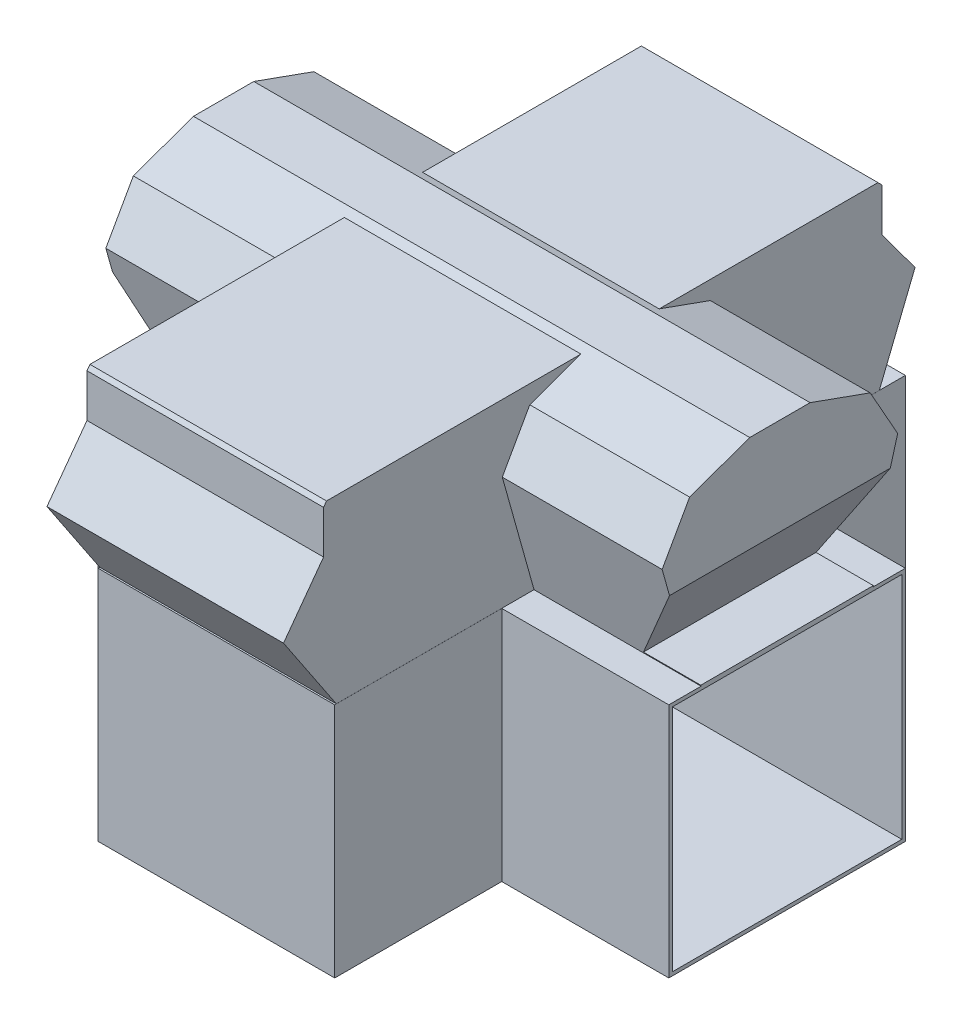
SolidWorks part; units mm, degrees
ref_plane "Front Plane" through (0, 0, 0) normal (0, 0, 1) x (1, 0, 0)
ref_plane "Top Plane" through (0, 0, 0) normal (0, 1, 0) x (1, 0, 0)
ref_plane "Right Plane" through (0, 0, 0) normal (1, 0, 0) x (0, 0, -1)
sketch "Sketch1" plane through (0, 0, 0) normal (0, 1, 0) x (1, 0, 0)
  line L0 (-111.4985, 263.0021) -> (-111.4985, 558.9121)
  line L1 (-111.4985, 558.9121) -> (307.6015, 558.9121)
  line L2 (307.6015, 558.9121) -> (307.6015, 263.0021)
  line L3 (307.6015, 263.0021) -> (603.5115, 263.0021)
  line L4 (603.5115, 263.0021) -> (603.5115, -156.0979)
  line L5 (603.5115, -156.0979) -> (307.6015, -156.0979)
  line L6 (307.6015, -156.0979) -> (307.6015, -452.0079)
  line L7 (307.6015, -452.0079) -> (-111.4985, -452.0079)
  line L8 (-111.4985, -452.0079) -> (-111.4985, -156.0979)
  line L9 (-111.4985, -156.0979) -> (-407.4085, -156.0979)
  line L10 (-407.4085, -156.0979) -> (-407.4085, 263.0021)
  line L11 (-407.4085, 263.0021) -> (-111.4985, 263.0021)
  point P11 (-259.4535, -156.0979)
  dimension "D1" = 1010.92
  dimension "D2" = 1010.92
  dimension "D3" = 419.1
  dimension "D4" = 419.1
extrude "Boss-Extrude1" add sketch "Sketch1" along normal blind 419.1
sketch "Sketch2" plane through (-407.4085, 0, 0) normal (-1, 0, 0) x (0, 0, 1)
  line L0 (-263.0021, 419.1) -> (-263.0021, 0) construction
  line L1 (-256.6521, 6.35) -> (149.7479, 6.35)
  line L2 (-256.6521, 6.35) -> (-256.6521, 412.75)
  line L3 (-256.6521, 412.75) -> (149.7479, 412.75)
  line L4 (149.7479, 6.35) -> (149.7479, 412.75)
  line L5 (-263.0021, 0) -> (156.0979, 0) construction
  dimension "D1" = 406.4
  dimension "D2" = 406.4
  dimension "D3" = 6.35
  dimension "D4" = 6.35
extrude "Cut-Extrude1" cut sketch "Sketch2" against normal blind 406.4
ref_plane "Plane1" through (98.0515, 0, 0) normal (-1, 0, 0) x (0, 0, 1)
mirror "Mirror1" about plane through (98.0515, 0, 0) normal (-1, 0, 0) of "Cut-Extrude1"
sketch "Sketch3" plane through (98.0515, 0, 0) normal (-1, 0, 0) x (0, 0, 1)
  line L0 (-53.4521, 278.7306) -> (-53.4521, 559.4694) construction
  line L2 (-263.0021, 419.1) -> (156.0979, 419.1) construction
  line L3 (-205.7901, 419.1) -> (98.8859, 419.1)
  line L4 (98.8859, 419.1) -> (155.1859, 620.0425)
  line L5 (155.1859, 620.0425) -> (106.482, 706.6608)
  line L6 (106.482, 706.6608) -> (0, 744.8644)
  line L7 (0, 744.8644) -> (-106.9041, 744.8644)
  line L8 (-213.3861, 706.6608) -> (-106.9041, 744.8644)
  line L9 (-262.09, 620.0425) -> (-213.3861, 706.6608)
  line L10 (-205.7901, 419.1) -> (-262.09, 620.0425)
  point P2 (-53.4521, 419.1)
  point P12 (-53.4521, 744.8644)
  point P15 (-53.4521, 419.1)
extrude "Boss-Extrude2" add sketch "Sketch3" along normal up to surface and the other way up to surface
sketch "Sketch4" plane through (0, 0, 0) normal (0, 0, 1) x (1, 0, 0)
  line L0 (-305.8085, 425.4541) -> (-394.7085, 577.8541)
  line L1 (-394.7085, 577.8541) -> (-394.7085, 796.5802)
  line L2 (-394.7085, 796.5802) -> (590.8115, 796.5802)
  line L3 (590.8115, 796.5802) -> (590.8115, 573.314)
  line L4 (590.8115, 573.314) -> (501.9115, 420.914)
  line L5 (501.9115, 420.914) -> (647.1891, 420.914)
  line L6 (647.1891, 420.914) -> (647.1891, 885.6356)
  line L7 (647.1891, 885.6356) -> (-516.8911, 876.8828)
  line L8 (-516.8911, 876.8828) -> (-501.7416, 425.4541)
  line L9 (-501.7416, 425.4541) -> (-305.8085, 425.4541)
  line L10 (-407.4085, 419.1) -> (-407.4085, 0) construction
  line L11 (603.5115, 419.1) -> (603.5115, 0) construction
  line L12 (603.5115, 412.75) -> (603.5115, 6.35) construction
  dimension "D1" = 101.6
  dimension "D2" = 101.6
  dimension "D3" = 12.7
  dimension "D4" = 12.7
  dimension "D5" = 152.4
  dimension "D6" = 152.4
extrude "Cut-Extrude2" cut sketch "Sketch4" against normal through all and the other way through all
sketch "Sketch5" plane through (0, 0, 0) normal (1, 0, 0) x (0, 0, -1)
  line L0 (-449.181, 419.2062) -> (-542.7052, 559.0693)
  line L1 (-542.7052, 559.0693) -> (-471.8211, 655.707)
  line L2 (-471.8211, 655.707) -> (-471.8211, 732.0002)
  line L3 (-471.8211, 732.0002) -> (-466.5564, 739.1776)
  line L4 (-466.5564, 739.1776) -> (510.3283, 739.1776)
  line L5 (510.3283, 739.1776) -> (517.5058, 732.0002)
  line L6 (517.5058, 732.0002) -> (517.5058, 655.707)
  line L7 (517.5058, 655.707) -> (576.0404, 576.0878)
  line L8 (576.0404, 576.0878) -> (512.7855, 419.2062)
  line L9 (512.7855, 419.2062) -> (-449.181, 419.2062)
extrude "Boss-Extrude3" add sketch "Sketch5" against normal up to surface and the other way up to surface up to face at (-111.4985, 209.55, 304.0529) other way up to face at (307.6015, 209.55, 304.0529)
